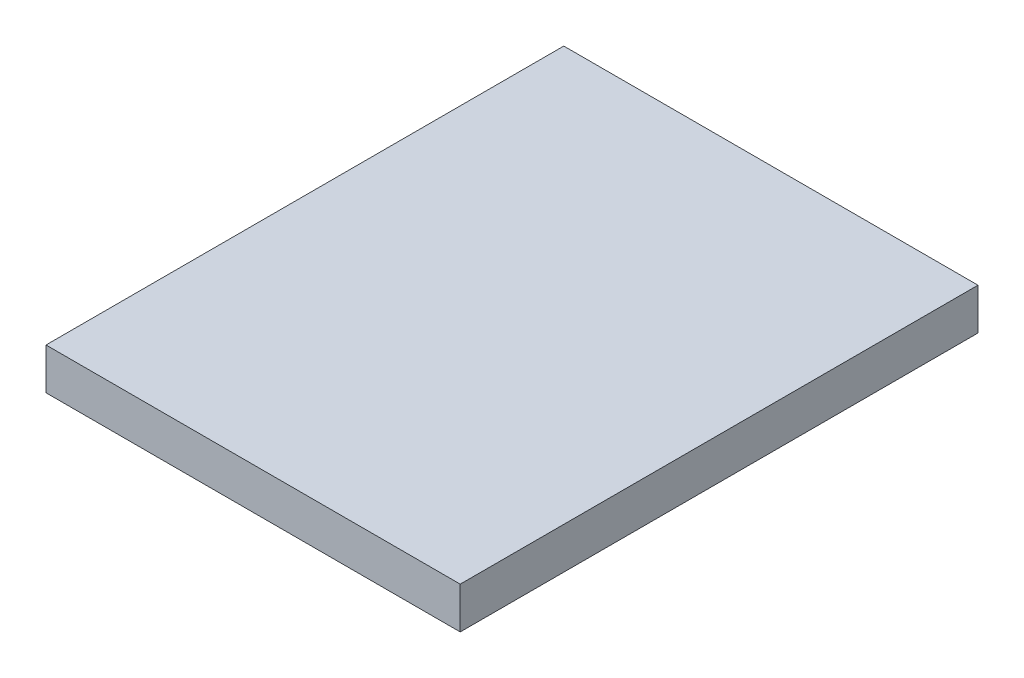
SolidWorks part; units mm, degrees
ref_plane "Front Plane" through (0, 0, 0) normal (0, 0, 1) x (1, 0, 0)
ref_plane "Top Plane" through (0, 0, 0) normal (0, 1, 0) x (1, 0, 0)
ref_plane "Right Plane" through (0, 0, 0) normal (1, 0, 0) x (0, 0, -1)
sketch "Sketch1" plane through (0, 0, 0) normal (0, 1, 0) x (1, 0, 0)
  line L1 (1000, 1250) -> (-1000, 1250)
  line L2 (1000, 1250) -> (1000, -1250)
  line L3 (1000, -1250) -> (-1000, -1250)
  line L4 (-1000, 1250) -> (-1000, -1250)
  line L5 (1000, 1250) -> (-1000, -1250) construction
  line L6 (1000, -1250) -> (-1000, 1250) construction
  point P0 (0, 0)
  dimension "D1" = 2000
  dimension "D2" = 2500
extrude "Boss-Extrude1" add sketch "Sketch1" along normal mid plane 200
